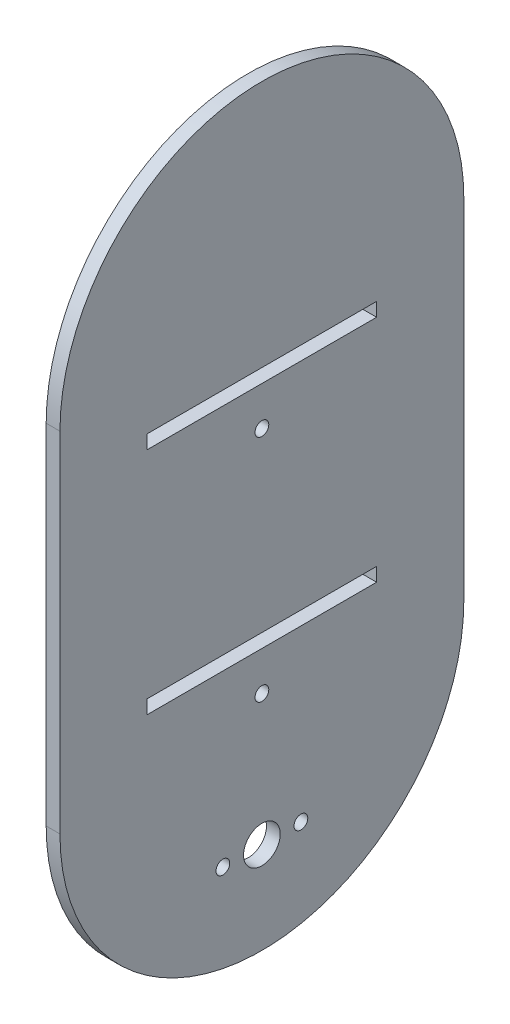
SolidWorks part; units mm, degrees
material "Acrylic (Medium-high impact)"
ref_plane "Front Plane" through (0, 0, 0) normal (0, 0, 1) x (1, 0, 0)
ref_plane "Top Plane" through (0, 0, 0) normal (0, 1, 0) x (1, 0, 0)
ref_plane "Right Plane" through (0, 0, 0) normal (1, 0, 0) x (0, 0, -1)
sketch "Sketch1" plane through (0, 0, 0) normal (1, 0, 0) x (0, 0, -1)
  line L0 (0, 188.1001) -> (0, -170.4231) construction
  line L1 (-136.2048, -10) -> (176.0962, -10) construction
  line L2 (-44, -120) -> (44, -120) construction
  line L3 (44, -120) -> (44, 0) construction
  line L4 (-44, -120) -> (-44, 0) construction
  line L5 (-148.8656, -60) -> (183.8334, -60) construction
  line L6 (-25, -10) -> (25, -10)
  line L7 (25, -10) -> (25, -13)
  line L8 (25, -13) -> (-25, -13)
  line L9 (-25, -10) -> (-25, -13)
  line L10 (-25, -60) -> (25, -60)
  line L11 (25, -60) -> (25, -63)
  line L12 (25, -63) -> (-25, -63)
  line L13 (-25, -60) -> (-25, -63)
  line L14 (-65.3115, -100) -> (74.1178, -100) construction
  line L15 (-8.5, -90.8423) -> (-8.5, -109.6029) construction
  line L16 (8.5, -90.8423) -> (8.5, -109.6029) construction
  line L17 (-44, 0) -> (-44, -76)
  line L18 (44, 0) -> (44, -76)
  arc A0 (44, 0) -> (-44, 0) centre (0, 0) ccw
  circle A1 centre (0, -21.5) radius 1.5
  circle A2 centre (0, -71.5) radius 1.5
  circle A3 centre (0, -100) radius 4
  circle A4 centre (-8.5, -100) radius 1.5
  circle A5 centre (8.5, -100) radius 1.5
  arc A6 (-44, -76) -> (44, -76) centre (0, -76) ccw
  point P11 (0, -120)
  point P18 (0, -13)
  point P19 (0, -10)
  point P23 (0, -60)
  point P25 (0, -63)
  dimension "D1" = 88
  dimension "D3" = 10
  dimension "D10" = 3
  dimension "D11" = 3
  dimension "D14" = 8
  dimension "D16" = 3
  dimension "D2" = 120
  dimension "D4" = 50
  dimension "D5" = 25
  dimension "D6" = 3
  dimension "D7" = 3
  dimension "D8" = 25
  dimension "D9" = 8.5
  dimension "D12" = 8.5
  dimension "D13" = 40
  dimension "D15" = 8.5
  dimension "D17" = 16
extrude "Boss-Extrude1" add sketch "Sketch1" along normal blind 3
